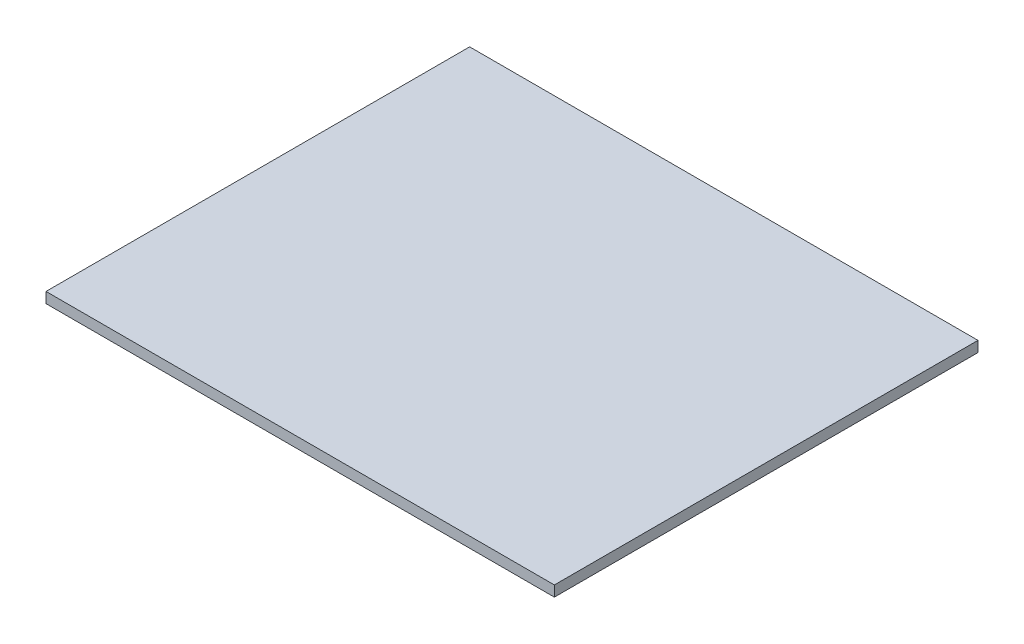
SolidWorks part; units mm, degrees
ref_plane "Front Plane" through (0, 0, 0) normal (0, 0, 1) x (1, 0, 0)
ref_plane "Top Plane" through (0, 0, 0) normal (0, 1, 0) x (1, 0, 0)
ref_plane "Right Plane" through (0, 0, 0) normal (1, 0, 0) x (0, 0, -1)
sketch "Sketch1" plane through (0, 0, 0) normal (0, 1, 0) x (1, 0, 0)
  line L1 (-76.2, 63.5) -> (76.2, 63.5)
  line L2 (-76.2, 63.5) -> (-76.2, -63.5)
  line L3 (-76.2, -63.5) -> (76.2, -63.5)
  line L4 (76.2, 63.5) -> (76.2, -63.5)
  line L5 (-76.2, 63.5) -> (76.2, -63.5) construction
  line L6 (-76.2, -63.5) -> (76.2, 63.5) construction
  point P0 (0, 0)
  dimension "D1" = 127
  dimension "D2" = 152.4
extrude "Boss-Extrude1" add sketch "Sketch1" along normal blind 3.175
